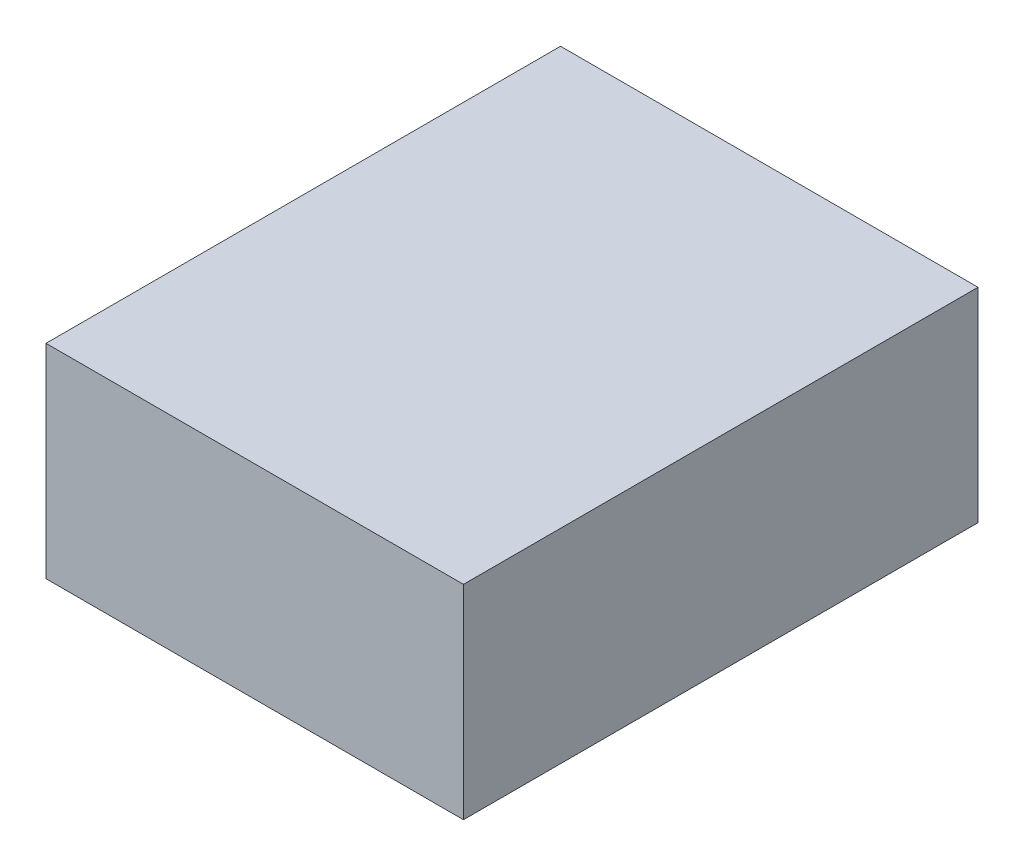
SolidWorks part; units mm, degrees
ref_plane "Front Plane" through (0, 0, 0) normal (0, 0, 1) x (1, 0, 0)
ref_plane "Top Plane" through (0, 0, 0) normal (0, 1, 0) x (1, 0, 0)
ref_plane "Right Plane" through (0, 0, 0) normal (1, 0, 0) x (0, 0, -1)
sketch "Sketch1" plane through (0, 0, 0) normal (0, 1, 0) x (1, 0, 0)
  line L1 (0, 0) -> (43, 0)
  line L2 (0, 0) -> (0, 53)
  line L3 (0, 53) -> (43, 53)
  line L4 (43, 0) -> (43, 53)
  dimension "D1" = 43
  dimension "D2" = 53
extrude "Boss-Extrude1" add sketch "Sketch1" along normal blind 21
